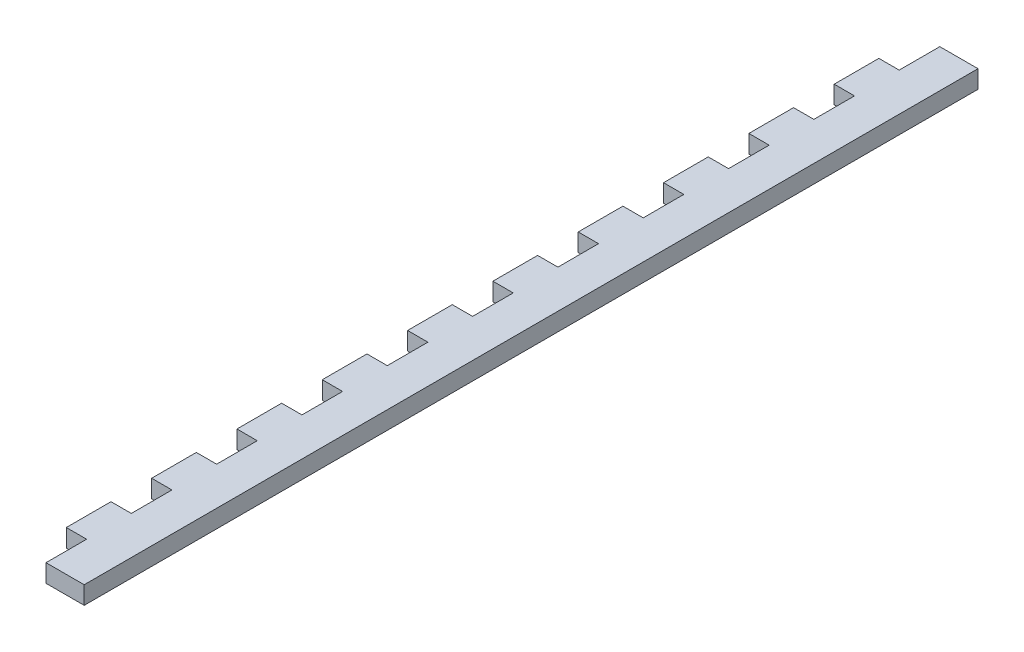
SolidWorks part; units mm, degrees
material "Acrylic (Medium-high impact)"
ref_plane "Front" through (0, 0, 0) normal (0, 0, 1) x (1, 0, 0)
ref_plane "Top" through (0, 0, 0) normal (0, 1, 0) x (1, 0, 0)
ref_plane "Right" through (0, 0, 0) normal (1, 0, 0) x (0, 0, -1)
sketch "Sketch1" plane through (0, 0, 0) normal (1, 0, 0) x (0, 0, -1)
  line L1 (-139.7, 142.875) -> (139.7, 142.875)
  line L2 (-139.7, 142.875) -> (-139.7, -142.875)
  line L3 (-139.7, -142.875) -> (139.7, -142.875)
  line L4 (139.7, 142.875) -> (139.7, -142.875)
  point P4 (-139.7, 0)
  point P6 (0, 142.875)
  dimension "D1" = 285.75
  dimension "D2" = 279.4
extrude "Boss-Extrude1" add sketch "Sketch1" along normal blind 5.588
sketch "Sketch2" plane through (5.588, 0, 0) normal (1, 0, 0) x (0, 0, -1)
  line L0 (139.7, -142.875) -> (139.7, 142.875) construction
  line L1 (-139.7, 142.875) -> (139.7, 142.875)
  line L2 (-139.7, 142.875) -> (-139.7, 137.287)
  line L3 (-139.7, 137.287) -> (139.7, 137.287)
  line L4 (139.7, 142.875) -> (139.7, 137.287)
  dimension "D1" = 5.588
extrude "Boss-Extrude2" add sketch "Sketch2" along normal blind 12.7
sketch "Sketch3" plane through (0, 0, 0) normal (-1, 0, 0) x (0, 0, 1)
  line L0 (-114.3, -85.725) -> (-25.4, -85.725)
  line L1 (-25.4, -111.125) -> (-114.3, -111.125)
  line L2 (12.7, 142.875) -> (12.7, -142.875) construction
  line L3 (-139.7, 142.875) -> (139.7, 142.875) construction
  line L4 (139.7, -142.875) -> (-139.7, -142.875) construction
  line L5 (139.7, 142.875) -> (139.7, -142.875) construction
  arc A0 (-25.4, -85.725) -> (-25.4, -111.125) centre (-25.4, -98.425) cw
  arc A1 (-114.3, -111.125) -> (-114.3, -85.725) centre (-114.3, -98.425) cw
  dimension "D1" = 25.4
  dimension "D3" = 88.9
  dimension "D2" = 38.1
  dimension "D4" = 127
  dimension "D5" = 44.45
extrude "Cut-Extrude1" cut sketch "Sketch3" against normal through all
sketch "Sketch4" plane through (0, 0, 0) normal (-1, 0, 0) x (0, 0, 1)
  line L0 (-113.03, 142.875) -> (-100.33, 142.875)
  line L1 (-139.7, 142.875) -> (-127, 142.875)
  line L2 (-139.7, 142.875) -> (-139.7, 137.287)
  line L3 (-139.7, 137.287) -> (-127, 137.287)
  line L4 (-127, 142.875) -> (-127, 137.287)
  line L5 (-113.03, 142.875) -> (-113.03, 137.287)
  line L6 (-113.03, 137.287) -> (-100.33, 137.287)
  line L7 (-100.33, 142.875) -> (-100.33, 137.287)
  line L8 (-86.36, 142.875) -> (-73.66, 142.875)
  line L9 (-86.36, 142.875) -> (-86.36, 137.287)
  line L10 (-86.36, 137.287) -> (-73.66, 137.287)
  line L11 (-73.66, 142.875) -> (-73.66, 137.287)
  line L12 (-59.69, 142.875) -> (-46.99, 142.875)
  line L13 (-59.69, 142.875) -> (-59.69, 137.287)
  line L14 (-59.69, 137.287) -> (-46.99, 137.287)
  line L15 (-46.99, 142.875) -> (-46.99, 137.287)
  line L16 (-33.02, 142.875) -> (-20.32, 142.875)
  line L17 (-33.02, 142.875) -> (-33.02, 137.287)
  line L18 (-33.02, 137.287) -> (-20.32, 137.287)
  line L19 (-20.32, 142.875) -> (-20.32, 137.287)
  line L20 (-6.35, 142.875) -> (6.35, 142.875)
  line L21 (-6.35, 142.875) -> (-6.35, 137.287)
  line L22 (-6.35, 137.287) -> (6.35, 137.287)
  line L23 (6.35, 142.875) -> (6.35, 137.287)
  line L24 (20.32, 142.875) -> (33.02, 142.875)
  line L25 (20.32, 142.875) -> (20.32, 137.287)
  line L26 (20.32, 137.287) -> (33.02, 137.287)
  line L27 (33.02, 142.875) -> (33.02, 137.287)
  line L28 (46.99, 142.875) -> (59.69, 142.875)
  line L29 (46.99, 142.875) -> (46.99, 137.287)
  line L30 (46.99, 137.287) -> (59.69, 137.287)
  line L31 (59.69, 142.875) -> (59.69, 137.287)
  line L32 (73.66, 142.875) -> (86.36, 142.875)
  line L33 (73.66, 142.875) -> (73.66, 137.287)
  line L34 (73.66, 137.287) -> (86.36, 137.287)
  line L35 (86.36, 142.875) -> (86.36, 137.287)
  line L36 (100.33, 142.875) -> (113.03, 142.875)
  line L37 (100.33, 142.875) -> (100.33, 137.287)
  line L38 (100.33, 137.287) -> (113.03, 137.287)
  line L39 (113.03, 142.875) -> (113.03, 137.287)
  line L40 (127, 142.875) -> (139.7, 142.875)
  line L41 (127, 142.875) -> (127, 137.287)
  line L42 (127, 137.287) -> (139.7, 137.287)
  line L43 (139.7, 142.875) -> (139.7, 137.287)
  line L69 (-139.7, 142.875) -> (139.7, 142.875)
  line L70 (-139.7, 142.875) -> (-139.7, 137.287)
  line L71 (-139.7, 137.287) -> (139.7, 137.287)
  line L72 (139.7, 142.875) -> (139.7, 137.287)
  line M73 (139.7, -142.875) -> (139.7, 142.875)
  line M74 (139.7, 142.875) -> (-139.7, 142.875)
  line M75 (-139.7, 142.875) -> (-139.7, -142.875)
  dimension "D1" = 5.588
  dimension "D2" = 12.7
  dimension "D3" = 11
sketch "Sketch5" plane through (0, 0, -139.7) normal (0, 0, -1) x (-1, 0, 0)
  line L1 (45.8749, 137.287) -> (-18.288, 137.287)
  line L2 (45.8749, 137.287) -> (45.8749, -231.4418)
  line L3 (45.8749, -231.4418) -> (-18.288, -231.4418)
  line L4 (-18.288, 137.287) -> (-18.288, -231.4418)
extrude "Cut-Extrude2" cut sketch "Sketch5" against normal through all
extrude "Cut-Extrude3" cut sketch "Sketch4" against normal blind 6.35 contours L7 L5 L6 M74 | L11 L9 L10 M74 | L15 L13 L14 M74 | L19 L17 L18 M74 | L23 L21 L22 M74 | L27 L25 L26 M74 | L31 L29 L30 M74 | L35 L33 L34 M74 | L39 L37 L38 M74 | L41 L42 M73 M74 | L4 L3 M74 M75 | L69
